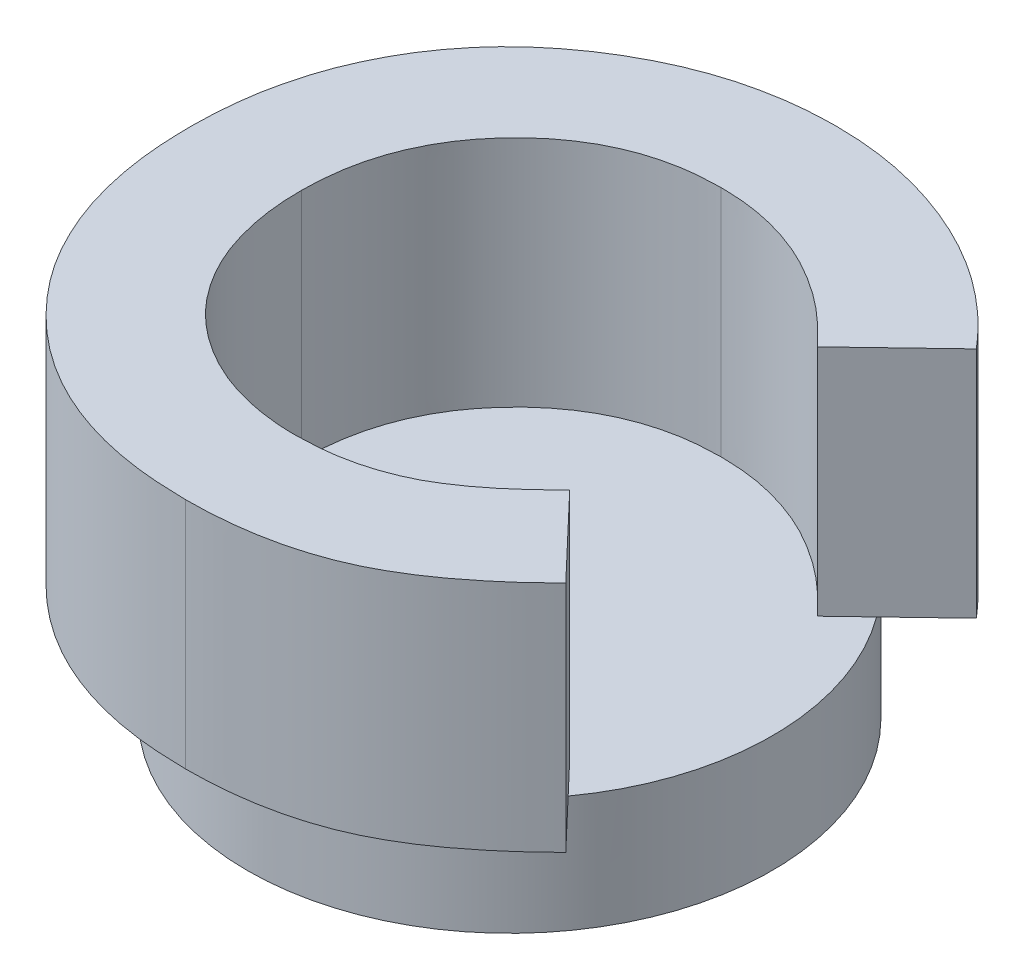
SolidWorks part; units mm, degrees
ref_plane "Front Plane" through (0, 0, 0) normal (0, 0, 1) x (1, 0, 0)
ref_plane "Top Plane" through (0, 0, 0) normal (0, 1, 0) x (1, 0, 0)
ref_plane "Right Plane" through (0, 0, 0) normal (1, 0, 0) x (0, 0, -1)
sketch "Sketch1" plane through (0, 0, 0) normal (0, 1, 0) x (1, 0, 0)
  circle A0 centre (0, 0) radius 22.5
  dimension "D1" = 45
extrude "Boss-Extrude1" add sketch "Sketch1" along normal blind 10
sketch "Sketch2" plane through (0, 10, 0) normal (0, 1, 0) x (1, 0, 0)
  text T0 "<b>C</b>" font "Century Gothic" height in points 200
extrude "Boss-Extrude2" add sketch "Sketch2" along normal blind 20
sketch "Sketch3" plane through (0, 0, 0) normal (0, -1, 0) x (1, 0, 0)
  line L0 (14.5514, 2.7786) -> (0, 30)
  line L1 (0, 30) -> (-14.5514, 2.7786)
  circle A0 centre (0, -5) radius 16.5
  circle A2 centre (0, 0) radius 22.5 construction
  circle A4 centre (0, 0) radius 21.5
  circle A5 centre (0, 0) radius 21.5
  dimension "D1" = 33
  dimension "D2" = 35
  dimension "D3" = 5
  dimension "D4" = 1
extrude "Cut-Extrude2" cut sketch "Sketch3" against normal blind 5 contours L0 A5 L1 A0 | A0
